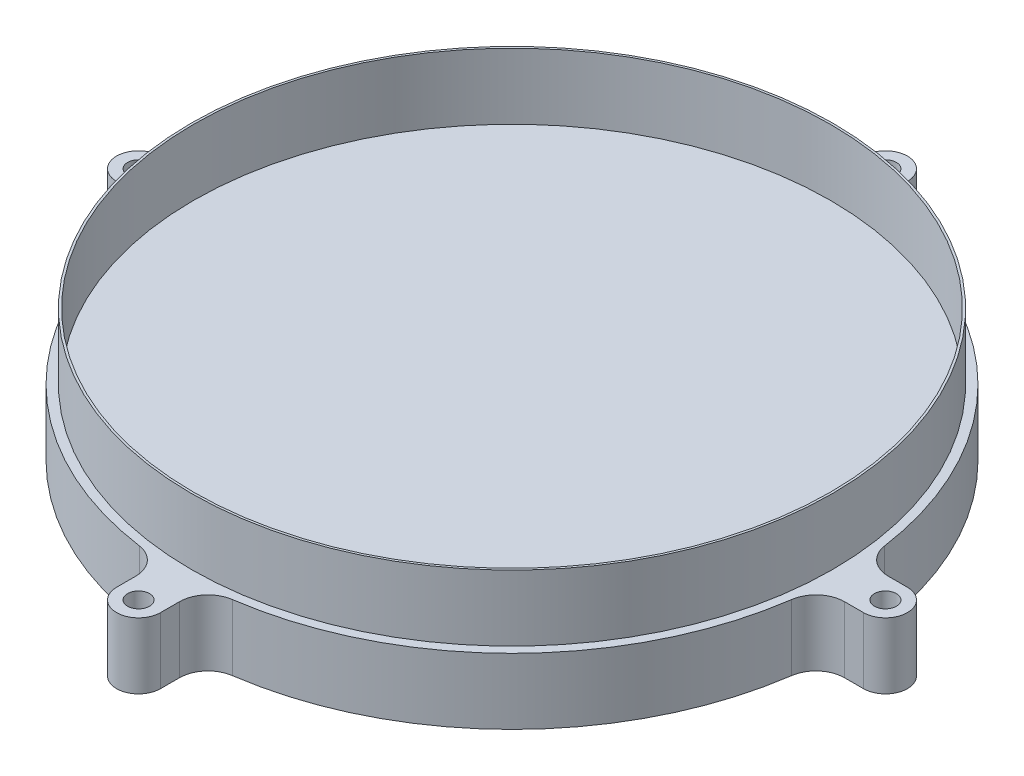
SolidWorks part; units mm, degrees
ref_plane "Front Plane" through (0, 0, 0) normal (0, 0, 1) x (1, 0, 0)
ref_plane "Top Plane" through (0, 0, 0) normal (0, 1, 0) x (1, 0, 0)
ref_plane "Right Plane" through (0, 0, 0) normal (1, 0, 0) x (0, 0, -1)
sketch "Sketch2" plane through (0, 0, 0) normal (0, 1, 0) x (1, 0, 0)
  line L0 (0, 0) -> (0, -224.3017) construction
  line L1 (0, 0) -> (0, 200) construction
  line L2 (0, 0) -> (207.2583, 0) construction
  line L3 (0, 0) -> (-200, 0) construction
  line L4 (20, 148.6607) -> (20, 168.6607)
  line L5 (-20, 148.6607) -> (-20, 168.6607)
  line L6 (148.6607, 20) -> (168.6607, 20)
  line L7 (148.6607, -20) -> (168.6607, -20)
  line L8 (20, -148.6607) -> (20, -168.6607)
  line L9 (-20, -148.6607) -> (-20, -168.6607)
  line L10 (-148.6607, -20) -> (-168.6607, -20)
  line L11 (-148.6607, 20) -> (-168.6607, 20)
  circle A0 centre (0, 0) radius 146
  circle A1 centre (0, 0) radius 145
  arc A3 (-20, 168.6607) -> (20, 168.6607) centre (0, 168.6607) cw
  circle A4 centre (0, 168.6607) radius 4.3737
  arc A5 (168.6607, 20) -> (168.6607, -20) centre (168.6607, 0) cw
  circle A6 centre (168.6607, 0) radius 4.3737
  arc A7 (20, -168.6607) -> (-20, -168.6607) centre (0, -168.6607) cw
  circle A8 centre (0, -168.6607) radius 4.3737
  arc A9 (-168.6607, -20) -> (-168.6607, 20) centre (-168.6607, 0) cw
  circle A10 centre (-168.6607, 0) radius 4.3737
  point P36 (0, 0)
  dimension "D1" = 290
  dimension "D2" = 292
  dimension "D4" = 4
extrude "Boss-Extrude2" add sketch "Sketch2" along normal blind 30 contours A1 | A0
sketch "Sketch3" plane through (0, 0, 0) normal (0, 1, 0) x (1, 0, 0)
  line L0 (0, 0) -> (211.9111, 0) construction
  line L1 (0, 0) -> (-205.2426, 0) construction
  line L2 (0, 0) -> (0, 170) construction
  line L3 (0, 0) -> (0, -200) construction
  line L4 (161.3691, 10) -> (170, 10)
  line L5 (161.3691, -10) -> (170, -10)
  line L6 (-10, 161.3691) -> (-10, 170)
  line L7 (10, 161.3691) -> (10, 170)
  line L8 (10, -161.3691) -> (10, -170)
  line L9 (-10, -161.3691) -> (-10, -170)
  line L10 (-161.3691, -10) -> (-170, -10)
  line L11 (-161.3691, 10) -> (-170, 10)
  arc A0 (-21.1656, 148.4992) -> (-148.4992, 21.1656) centre (0, 0) ccw
  circle A1 centre (0, 170) radius 5
  arc A2 (-10, 170) -> (10, 170) centre (0, 170) cw
  arc A3 (10, 161.3691) -> (21.1656, 148.4992) centre (23, 161.3691) ccw
  arc A4 (-10, 161.3691) -> (-21.1656, 148.4992) centre (-23, 161.3691) cw
  arc A5 (170, 10) -> (170, -10) centre (170, 0) cw
  arc A6 (161.3691, 10) -> (148.4992, 21.1656) centre (161.3691, 23) cw
  circle A7 centre (170, 0) radius 5
  arc A8 (161.3691, -10) -> (148.4992, -21.1656) centre (161.3691, -23) ccw
  arc A9 (10, -170) -> (-10, -170) centre (0, -170) cw
  arc A10 (10, -161.3691) -> (21.1656, -148.4992) centre (23, -161.3691) cw
  circle A11 centre (0, -170) radius 5
  arc A12 (-10, -161.3691) -> (-21.1656, -148.4992) centre (-23, -161.3691) ccw
  arc A13 (-170, -10) -> (-170, 10) centre (-170, 0) cw
  arc A14 (-161.3691, -10) -> (-148.4992, -21.1656) centre (-161.3691, -23) cw
  circle A15 centre (-170, 0) radius 5
  arc A16 (-161.3691, 10) -> (-148.4992, 21.1656) centre (-161.3691, 23) ccw
  arc A17 (-148.4992, -21.1656) -> (-21.1656, -148.4992) centre (0, 0) ccw
  arc A18 (148.4992, 21.1656) -> (21.1656, 148.4992) centre (0, 0) ccw
  arc A19 (21.1656, -148.4992) -> (148.4992, -21.1656) centre (0, 0) ccw
  point P53 (0, 0)
  dimension "D1" = 300
  dimension "D4" = 10
  dimension "D2" = 4
extrude "Boss-Extrude4" add sketch "Sketch3" against normal blind 30
sketch "Sketch4" plane through (0, -30, 0) normal (0, -1, 0) x (1, 0, 0)
  line L0 (0, 0) -> (0, 219.6894) construction
  line L1 (0, 0) -> (0, -213.8257) construction
  line L2 (0, 0) -> (-191.8942, 0) construction
  line L3 (0, 0) -> (202.1981, 0) construction
  line L4 (5, -140.7151) -> (-5, -140.7151)
  line L5 (5, -140.7151) -> (5, -9.9236)
  line L6 (-5, -140.7151) -> (-5, -9.9236)
  line L7 (5, -9.9236) -> (-5, -9.9236)
  dimension "D1" = 5
  dimension "D2" = 5
